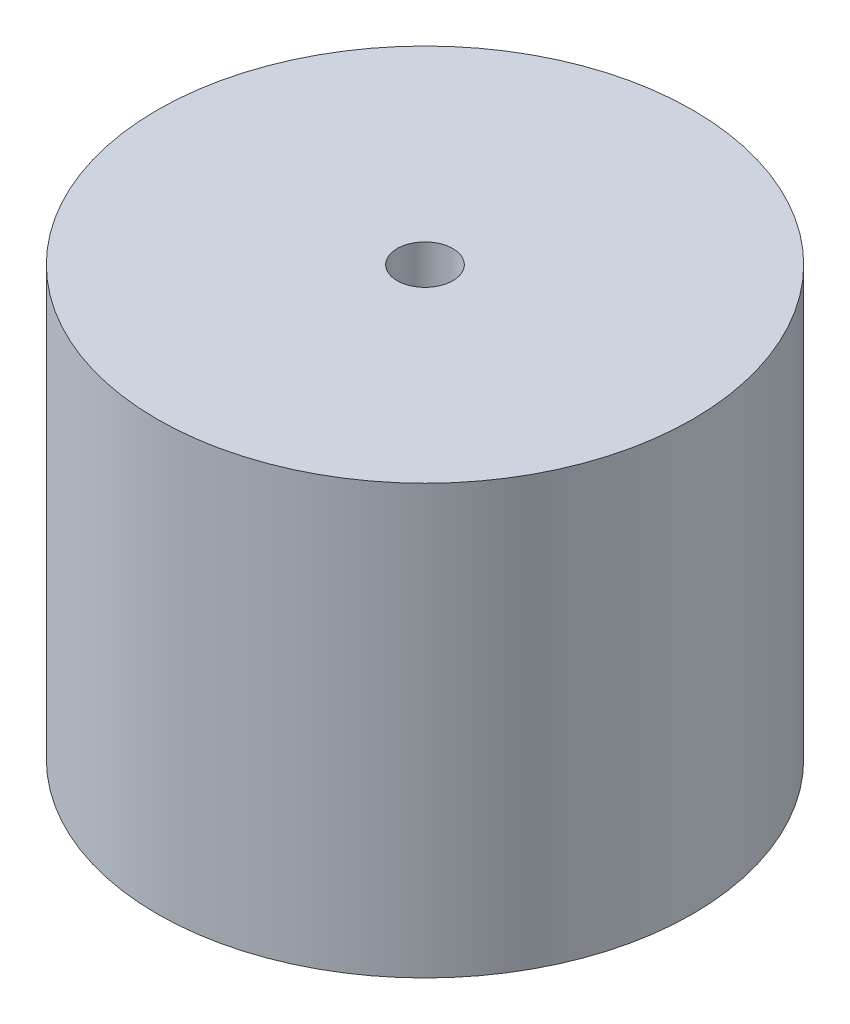
SolidWorks part; units mm, degrees
ref_plane "Front Plane" through (0, 0, 0) normal (0, 0, 1) x (1, 0, 0)
ref_plane "Top Plane" through (0, 0, 0) normal (0, 1, 0) x (1, 0, 0)
ref_plane "Right Plane" through (0, 0, 0) normal (1, 0, 0) x (0, 0, -1)
sketch "Sketch1" plane through (0, 0, 0) normal (0, 1, 0) x (1, 0, 0)
  circle A1 centre (-32.44, -6.2787) radius 0.3302
  circle A3 centre (-32.44, -6.2787) radius 3.175
extrude "Boss-Extrude2" add sketch "Sketch1" along normal blind 2.54
sketch "Sketch3" plane through (0, 0, 0) normal (0, -1, 0) x (1, 0, 0)
  circle A0 centre (-32.44, 6.2787) radius 3.175
extrude "Boss-Extrude3" add sketch "Sketch3" along normal blind 2.54
